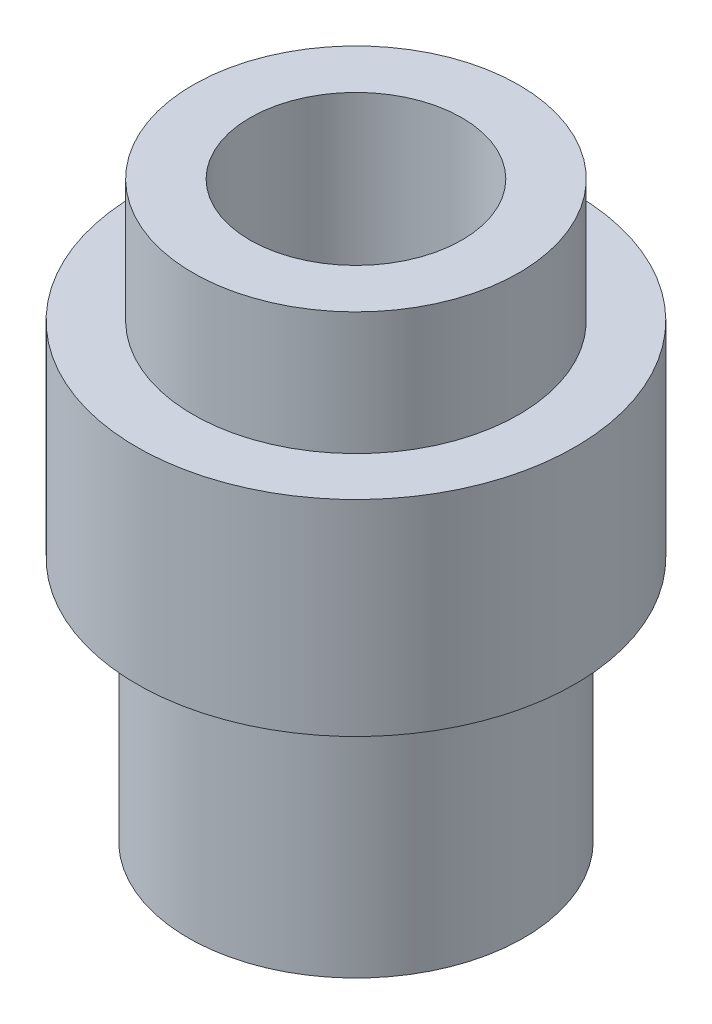
SolidWorks part; units mm, degrees
ref_plane "Front Plane" through (0, 0, 0) normal (0, 0, 1) x (1, 0, 0)
ref_plane "Top Plane" through (0, 0, 0) normal (0, 1, 0) x (1, 0, 0)
ref_plane "Right Plane" through (0, 0, 0) normal (1, 0, 0) x (0, 0, -1)
sketch "Sketch2" plane through (0, 0, 0) normal (0, 0, 1) x (1, 0, 0)
  line L0 (3.7601, 0) -> (3.7601, 5.5)
  line L1 (3.7601, 5.5) -> (4.91, 5.5)
  line L2 (4.91, 5.5) -> (4.91, 10.1)
  line L3 (4.91, 10.1) -> (3.65, 10.1)
  line L4 (2.375, 12.85) -> (2.375, 3.427)
  line L5 (2.375, 3.427) -> (0, 2)
  line L6 (0, 2) -> (0, 0)
  line L7 (3.7601, 0) -> (0, 0)
  line L9 (2.375, 12.85) -> (3.65, 12.85)
  line L10 (3.65, 12.85) -> (3.65, 10.1)
  line L11 (0, 0) -> (0, 10.5375) construction
  dimension "D1" = 3.7601
  dimension "D2" = 5.5
  dimension "D3" = 4.6
  dimension "D4" = 2
  dimension "D5" = 3.65
  dimension "D6" = 2.375
  dimension "D8" = 4.91
  dimension "D9" = 2.75
  dimension "D10" = 59
revolve "Revolve1" add sketch "Sketch2" angle 360 about L11
